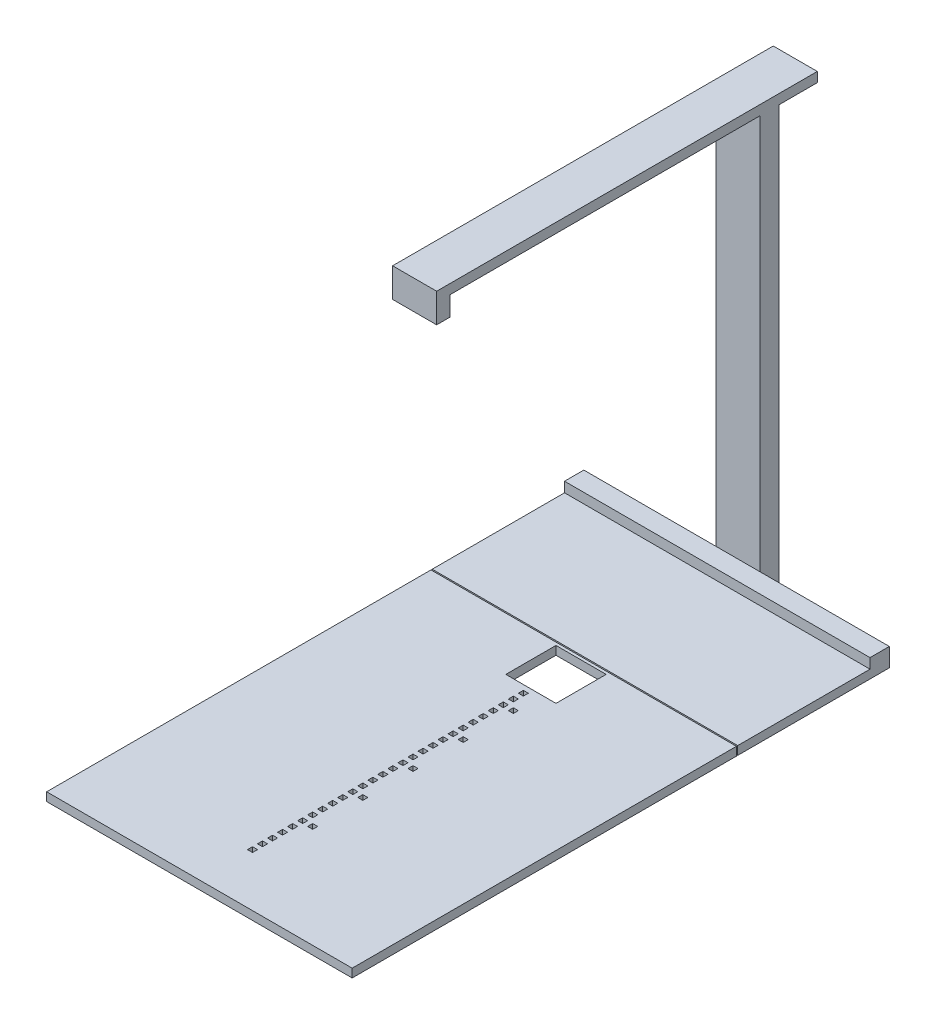
SolidWorks part; units mm, degrees
ref_plane "Front Plane" through (0, 0, 0) normal (0, 0, 1) x (1, 0, 0)
ref_plane "Top Plane" through (0, 0, 0) normal (0, 1, 0) x (1, 0, 0)
ref_plane "Right Plane" through (0, 0, 0) normal (1, 0, 0) x (0, 0, -1)
sketch "Sketch1" plane through (0, 0, 0) normal (0, 1, 0) x (1, 0, 0)
  line L0 (-5, -90) -> (5, -90)
  line L1 (-305, 55.73) -> (304, 55.73)
  line L2 (-305, 55.73) -> (-305, -710.27)
  line L3 (-305, -710.27) -> (304, -710.27)
  line L4 (304, 55.73) -> (304, -710.27)
  line L5 (-50, 50) -> (50, 50)
  line L6 (-50, 50) -> (-50, -50)
  line L7 (-50, -50) -> (50, -50)
  line L8 (50, 50) -> (50, -50)
  line L9 (-5, -60) -> (5, -60)
  line L10 (-5, -60) -> (-5, -70)
  line L11 (-5, -70) -> (5, -70)
  line L12 (5, -60) -> (5, -70)
  line L13 (5, -80) -> (5, -90)
  line L14 (-5, -80) -> (5, -80)
  line L15 (-5, -80) -> (-5, -90)
  line L16 (-5, -110) -> (5, -110)
  line L17 (5, -100) -> (5, -110)
  line L18 (-5, -100) -> (5, -100)
  line L19 (-5, -100) -> (-5, -110)
  line L20 (-5, -130) -> (5, -130)
  line L21 (5, -120) -> (5, -130)
  line L22 (-5, -120) -> (5, -120)
  line L23 (-5, -120) -> (-5, -130)
  line L24 (-5, -150) -> (5, -150)
  line L25 (5, -140) -> (5, -150)
  line L26 (-5, -140) -> (5, -140)
  line L27 (-5, -140) -> (-5, -150)
  line L28 (-5, -170) -> (5, -170)
  line L29 (5, -160) -> (5, -170)
  line L30 (-5, -160) -> (5, -160)
  line L31 (-5, -160) -> (-5, -170)
  line L32 (-5, -190) -> (5, -190)
  line L33 (5, -180) -> (5, -190)
  line L34 (-5, -180) -> (5, -180)
  line L35 (-5, -180) -> (-5, -190)
  line L36 (-5, -210) -> (5, -210)
  line L37 (5, -200) -> (5, -210)
  line L38 (-5, -200) -> (5, -200)
  line L39 (-5, -200) -> (-5, -210)
  line L40 (-5, -230) -> (5, -230)
  line L41 (5, -220) -> (5, -230)
  line L42 (-5, -220) -> (5, -220)
  line L43 (-5, -220) -> (-5, -230)
  line L44 (-5, -250) -> (5, -250)
  line L45 (5, -240) -> (5, -250)
  line L46 (-5, -240) -> (5, -240)
  line L47 (-5, -240) -> (-5, -250)
  line L48 (-5, -270) -> (5, -270)
  line L49 (5, -260) -> (5, -270)
  line L50 (-5, -260) -> (5, -260)
  line L51 (-5, -260) -> (-5, -270)
  line L52 (-5, -290) -> (5, -290)
  line L53 (5, -280) -> (5, -290)
  line L54 (-5, -280) -> (5, -280)
  line L55 (-5, -280) -> (-5, -290)
  line L56 (-5, -310) -> (5, -310)
  line L57 (5, -300) -> (5, -310)
  line L58 (-5, -300) -> (5, -300)
  line L59 (-5, -300) -> (-5, -310)
  line L60 (-5, -330) -> (5, -330)
  line L61 (5, -320) -> (5, -330)
  line L62 (-5, -320) -> (5, -320)
  line L63 (-5, -320) -> (-5, -330)
  line L64 (-5, -350) -> (5, -350)
  line L65 (5, -340) -> (5, -350)
  line L66 (-5, -340) -> (5, -340)
  line L67 (-5, -340) -> (-5, -350)
  line L68 (-5, -370) -> (5, -370)
  line L69 (5, -360) -> (5, -370)
  line L70 (-5, -360) -> (5, -360)
  line L71 (-5, -360) -> (-5, -370)
  line L72 (-5, -390) -> (5, -390)
  line L73 (5, -380) -> (5, -390)
  line L74 (-5, -380) -> (5, -380)
  line L75 (-5, -380) -> (-5, -390)
  line L76 (-5, -410) -> (5, -410)
  line L77 (5, -400) -> (5, -410)
  line L78 (-5, -400) -> (5, -400)
  line L79 (-5, -400) -> (-5, -410)
  line L80 (-5, -430) -> (5, -430)
  line L81 (5, -420) -> (5, -430)
  line L82 (-5, -420) -> (5, -420)
  line L83 (-5, -420) -> (-5, -430)
  line L84 (-5, -450) -> (5, -450)
  line L85 (5, -440) -> (5, -450)
  line L86 (-5, -440) -> (5, -440)
  line L87 (-5, -440) -> (-5, -450)
  line L88 (-5, -470) -> (5, -470)
  line L89 (5, -460) -> (5, -470)
  line L90 (-5, -460) -> (5, -460)
  line L91 (-5, -460) -> (-5, -470)
  line L92 (-5, -490) -> (5, -490)
  line L93 (5, -480) -> (5, -490)
  line L94 (-5, -480) -> (5, -480)
  line L95 (-5, -480) -> (-5, -490)
  line L96 (-5, -510) -> (5, -510)
  line L97 (5, -500) -> (5, -510)
  line L98 (-5, -500) -> (5, -500)
  line L99 (-5, -500) -> (-5, -510)
  line L100 (-5, -530) -> (5, -530)
  line L101 (5, -520) -> (5, -530)
  line L102 (-5, -520) -> (5, -520)
  line L103 (-5, -520) -> (-5, -530)
  line L104 (-5, -550) -> (5, -550)
  line L105 (5, -540) -> (5, -550)
  line L106 (-5, -540) -> (5, -540)
  line L107 (-5, -540) -> (-5, -550)
  line L108 (-5, -570) -> (5, -570)
  line L109 (5, -560) -> (5, -570)
  line L110 (-5, -560) -> (5, -560)
  line L111 (-5, -560) -> (-5, -570)
  line L112 (-5, -590) -> (5, -590)
  line L113 (5, -580) -> (5, -590)
  line L114 (-5, -580) -> (5, -580)
  line L115 (-5, -580) -> (-5, -590)
  line L116 (-5, -610) -> (5, -610)
  line L117 (5, -600) -> (5, -610)
  line L118 (-5, -600) -> (5, -600)
  line L119 (-5, -600) -> (-5, -610)
  line L121 (15, -100) -> (25, -100)
  line L122 (15, -100) -> (15, -110)
  line L123 (25, -100) -> (25, -110)
  line L124 (15, -110) -> (25, -110)
  line L125 (15, -200) -> (25, -200)
  line L126 (15, -200) -> (15, -210)
  line L127 (15, -210) -> (25, -210)
  line L128 (25, -200) -> (25, -210)
  line L129 (15, -300) -> (25, -300)
  line L130 (15, -300) -> (15, -310)
  line L131 (25, -300) -> (25, -310)
  line L132 (15, -310) -> (25, -310)
  line L133 (15, -400) -> (25, -400)
  line L134 (25, -400) -> (25, -410)
  line L135 (15, -410) -> (25, -410)
  line L136 (15, -400) -> (15, -410)
  line L137 (15, -500) -> (25, -500)
  line L138 (25, -500) -> (25, -510)
  line L139 (15, -510) -> (25, -510)
  line L140 (15, -500) -> (15, -510)
  dimension "D1" = 609
  dimension "D2" = 766
  dimension "D3" = 100
  dimension "D4" = 100
  dimension "D5" = 50
  dimension "D6" = 50
  dimension "D7" = 5.73
  dimension "D8" = 255
  dimension "D9" = 10
  dimension "D10" = 10
  dimension "D11" = 60
  dimension "D12" = 5
  dimension "D14" = 80
  dimension "D15" = 2
  dimension "D16" = 100
  dimension "D17" = 10
  dimension "D19" = 100
  dimension "D20" = 10
  dimension "D22" = 100
  dimension "D23" = 10
  dimension "D24" = 2
  dimension "D25" = 100
  dimension "D26" = 10
  dimension "D28" = 100
  dimension "D29" = 10
  dimension "D13" = 28
  dimension "D18" = 2
  dimension "D21" = 2
  dimension "D27" = 2
extrude "Boss-Extrude1" add sketch "Sketch1" along normal blind 17
sketch "Sketch2" plane through (0, 0, 0) normal (0, -1, 0) x (-1, 0, 0)
  line L0 (-304, 55.73) -> (305, 55.73) construction
  line L1 (-304, 360.53) -> (305, 360.53)
  line L2 (-304, 360.53) -> (-304, 58.27)
  line L3 (-304, 58.27) -> (305, 58.27)
  line L4 (305, 360.53) -> (305, 58.27)
  line L6 (305, 55.73) -> (305, -710.27) construction
  dimension "D1" = 2.54
  dimension "D2" = 302.26
  dimension "D3" = 609
extrude "Boss-Extrude2" add sketch "Sketch2" against normal up to surface (17 mm away) separate body up to face at (20, 17, 405)
sketch "Sketch3" plane through (0, 17, 0) normal (0, 1, 0) x (1, 0, 0)
  line L0 (-305, 58.27) -> (-305, 360.53) construction
  line L1 (304, 360.53) -> (-305, 360.53)
  line L2 (304, 360.53) -> (304, 322.03)
  line L3 (304, 322.03) -> (-305, 322.03)
  line L4 (-305, 360.53) -> (-305, 322.03)
  dimension "D1" = 38.5
extrude "Boss-Extrude3" add sketch "Sketch3" along normal blind 20
sketch "Sketch4" plane through (0, 0, 0) normal (0, -1, 0) x (1, 0, 0)
  line L0 (-305, -360.53) -> (304, -360.53) construction
  line L1 (-41.475, -360.53) -> (46.325, -360.53)
  line L2 (-41.475, -360.53) -> (-41.475, -398.43)
  line L3 (-41.475, -398.43) -> (46.325, -398.43)
  line L4 (46.325, -360.53) -> (46.325, -398.43)
  line L5 (-305, -58.27) -> (-305, -360.53) construction
  dimension "D1" = 37.9
  dimension "D2" = 87.8
  dimension "D3" = 263.525
extrude "Boss-Extrude4" add sketch "Sketch4" against normal blind 824.4
sketch "Sketch5" plane through (0, 824.4, 0) normal (0, 1, 0) x (1, 0, 0)
  line L0 (-41.475, 398.43) -> (46.325, 398.43) construction
  line L1 (-41.475, 474.63) -> (46.325, 474.63)
  line L2 (-41.475, 474.63) -> (-41.475, -284.195)
  line L3 (-41.475, -284.195) -> (46.325, -284.195)
  line L4 (46.325, 474.63) -> (46.325, -284.195)
  dimension "D1" = 76.2
  dimension "D2" = 758.825
extrude "Boss-Extrude5" add sketch "Sketch5" along normal blind 19.4
sketch "Sketch6" plane through (0, 824.4, 0) normal (0, -1, 0) x (1, 0, 0)
  line L0 (46.325, 284.195) -> (46.325, -360.53) construction
  line L1 (-41.475, 284.195) -> (46.325, 284.195)
  line L2 (-41.475, 284.195) -> (-41.475, 257.195)
  line L3 (-41.475, 257.195) -> (46.325, 257.195)
  line L4 (46.325, 284.195) -> (46.325, 257.195)
  dimension "D1" = 27
extrude "Boss-Extrude6" add sketch "Sketch6" along normal blind 38.7
sketch "Sketch7" plane through (0, 0, 284.195) normal (0, 0, 1) x (1, 0, 0)
  line L0 (2.425, 843.8) -> (2.425, 785.7) construction
  line L1 (-41.475, 843.8) -> (46.325, 843.8) construction
  line L2 (46.325, 785.7) -> (-41.475, 785.7) construction
  point P6 (2.425, 814.75)
  point P7 (-83.7816, 871.0382)
